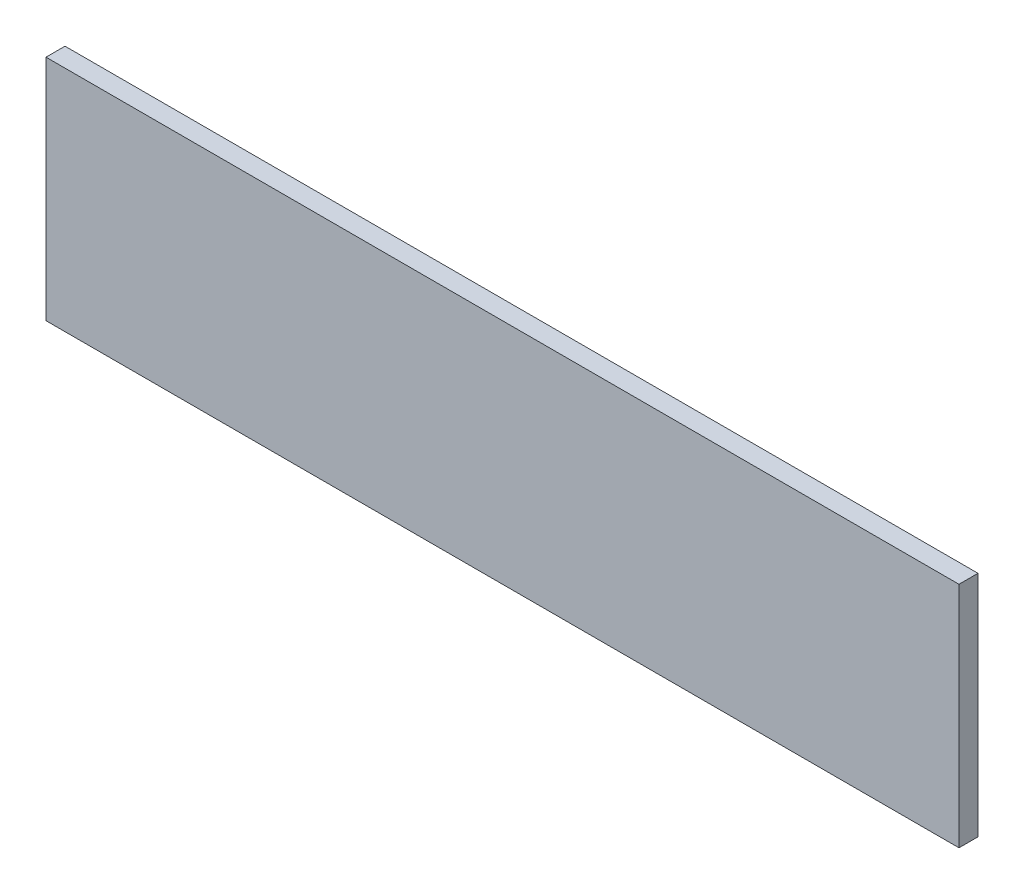
SolidWorks part; units mm, degrees
ref_plane "Front Plane" through (0, 0, 0) normal (0, 0, 1) x (1, 0, 0)
ref_plane "Top Plane" through (0, 0, 0) normal (0, 1, 0) x (1, 0, 0)
ref_plane "Right Plane" through (0, 0, 0) normal (1, 0, 0) x (0, 0, -1)
sketch "Sketch1" plane through (0, 0, 0) normal (0, 0, 1) x (1, 0, 0)
  line L1 (0, 0) -> (304.8, 0)
  line L2 (0, 0) -> (0, 76.2)
  line L3 (0, 76.2) -> (304.8, 76.2)
  line L4 (304.8, 0) -> (304.8, 76.2)
  dimension "D1" = 76.2
  dimension "D2" = 304.8
extrude "Boss-Extrude1" add sketch "Sketch1" along normal blind 6.35
